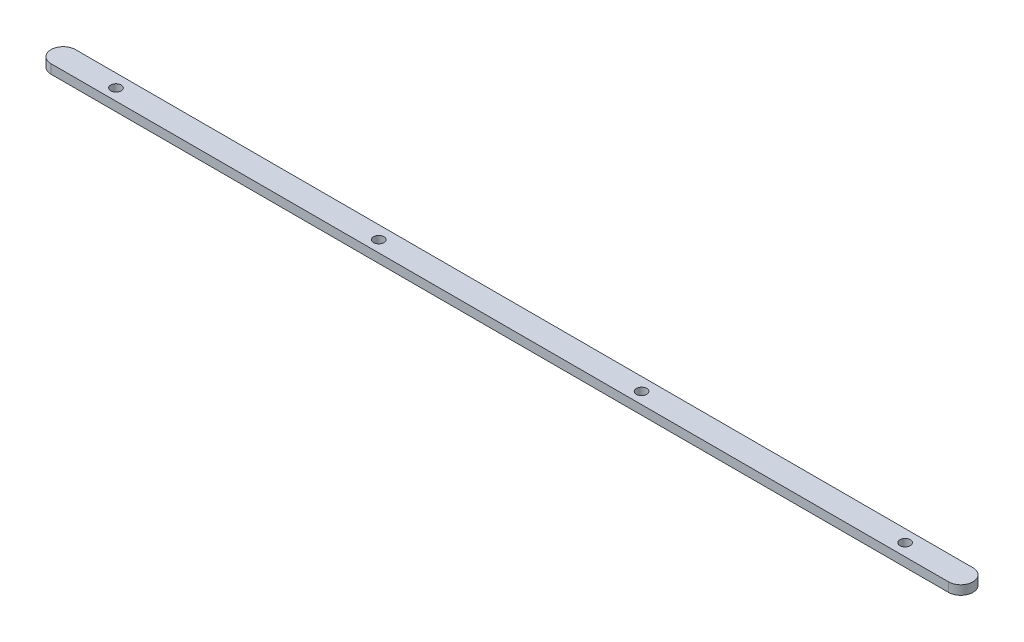
SolidWorks part; units mm, degrees
ref_plane "Front Plane" through (0, 0, 0) normal (0, 0, 1) x (1, 0, 0)
ref_plane "Top Plane" through (0, 0, 0) normal (0, 1, 0) x (1, 0, 0)
ref_plane "Right Plane" through (0, 0, 0) normal (1, 0, 0) x (0, 0, -1)
sketch "Sketch2" plane through (0, 0, 0) normal (0, 1, 0) x (1, 0, 0)
  line L0 (-129.9444, 0.1845) -> (163.755, 0.1845)
  line L1 (163.755, 8.1845) -> (-129.9444, 8.1845)
  circle A0 centre (145.5556, 4.1845) radius 1.7
  circle A1 centre (59.5556, 3.9345) radius 1.7
  circle A2 centre (-112.4444, 3.9345) radius 1.7
  circle A3 centre (-26.4444, 3.9345) radius 1.7
  arc A4 (-129.9444, 8.1845) -> (-133.9444, 4.1845) centre (-129.9444, 4.1845) ccw
  arc A5 (-133.9444, 4.1845) -> (-129.9444, 0.1845) centre (-129.9444, 4.1845) ccw
  arc A6 (163.755, 0.1845) -> (167.755, 4.1845) centre (163.755, 4.1845) ccw
  arc A7 (167.755, 4.1845) -> (163.755, 8.1845) centre (163.755, 4.1845) ccw
extrude "Boss-Extrude1" add sketch "Sketch2" along normal blind 3
